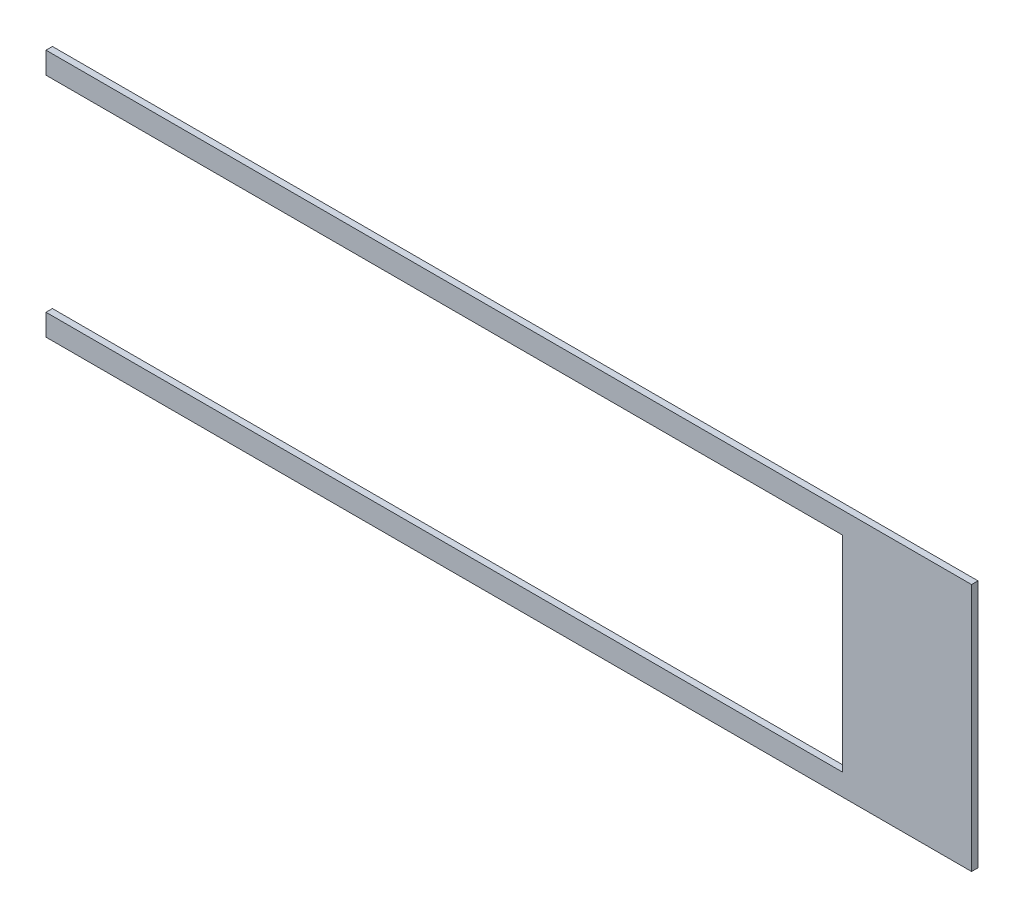
SolidWorks part; units mm, degrees
ref_plane "Front" through (0, 0, 0) normal (0, 0, 1) x (1, 0, 0)
ref_plane "Top" through (0, 0, 0) normal (0, 1, 0) x (1, 0, 0)
ref_plane "Right" through (0, 0, 0) normal (1, 0, 0) x (0, 0, -1)
sketch "Sketch1" plane through (0, 0, 0) normal (0, 0, 1) x (1, 0, 0)
  line L0 (-228.7016, -61.4172) -> (228.7016, -61.4172)
  line L1 (228.7016, -61.4172) -> (228.7016, 61.4172)
  line L2 (228.7016, 61.4172) -> (-228.7016, 61.4172)
  line L3 (-228.7016, 61.4172) -> (-228.7016, 50.6984)
  line L4 (-228.7016, 50.6984) -> (164.9984, 50.6984)
  line L5 (164.9984, 50.6984) -> (164.9984, -50.7492)
  line L6 (164.9984, -50.7492) -> (-228.7016, -50.7492)
  line L7 (-228.7016, -50.7492) -> (-228.7016, -61.4172)
extrude "Boss-Extrude1" add sketch "Sketch1" along normal blind 3.175
